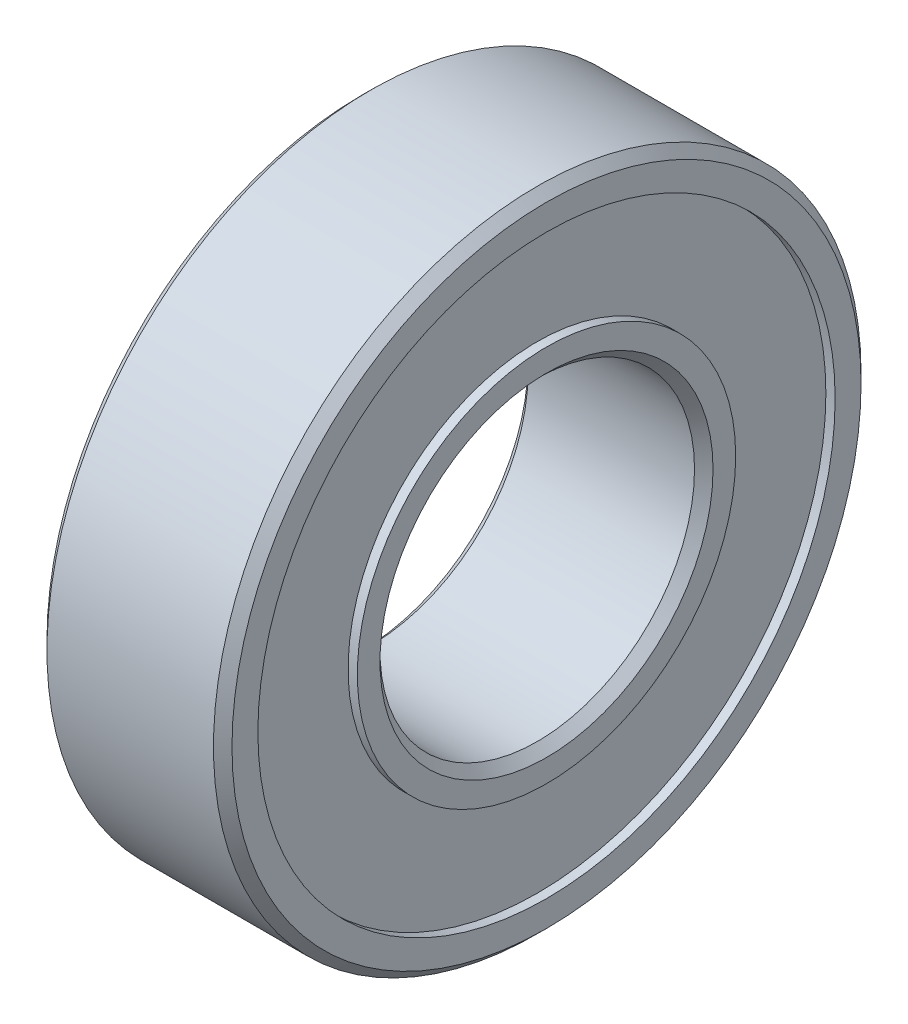
SolidWorks part; units mm, degrees
ref_plane "Front Plane" through (0, 0, 0) normal (0, 0, 1) x (1, 0, 0)
ref_plane "Top Plane" through (0, 0, 0) normal (0, 1, 0) x (1, 0, 0)
ref_plane "Right Plane" through (0, 0, 0) normal (1, 0, 0) x (0, 0, -1)
sketch "Sketch1" plane through (0, 0, 0) normal (1, 0, 0) x (0, 0, -1)
  circle A0 centre (0, 0) radius 8.5
  circle A1 centre (0, 0) radius 17.5
  dimension "D1" = 17
  dimension "D2" = 35
extrude "Boss-Extrude1" add sketch "Sketch1" along normal blind 10
chamfer "Chamfer1" distance 0.5 angle 45 4 edges at (0, 0, -8.5) (0, 0, -17.5) (10, 0, -8.5) (10, 0, -17.5)
sketch "Sketch2" plane through (10, 0, 0) normal (1, 0, 0) x (0, 0, -1)
  circle A0 centre (0, 0) radius 15.6
  circle A1 centre (0, 0) radius 10.225
  dimension "D1" = 20.45
  dimension "D2" = 31.2
extrude "Cut-Extrude1" cut sketch "Sketch2" against normal blind 0.5
sketch "Sketch3" plane through (0, 0, 0) normal (-1, 0, 0) x (0, 0, 1)
  circle A1 centre (0, 0) radius 10.225
  circle A2 centre (0, 0) radius 10.225
  circle A3 centre (0, 0) radius 15.6
  circle A4 centre (0, 0) radius 15.6
  dimension "D1" = 0
  dimension "D2" = 0
extrude "Cut-Extrude2" cut sketch "Sketch3" against normal blind 0.5
